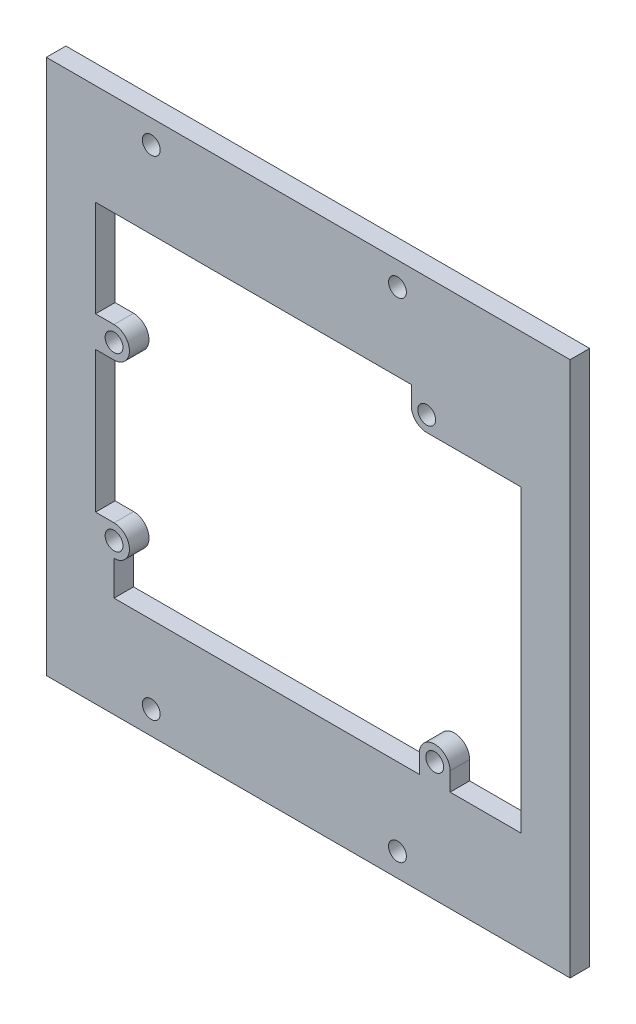
SolidWorks part; units mm, degrees
material "6061-T6 (SS)"
ref_plane "Front Plane" through (0, 0, 0) normal (0, 0, 1) x (1, 0, 0)
ref_plane "Top Plane" through (0, 0, 0) normal (0, 1, 0) x (1, 0, 0)
ref_plane "Right Plane" through (0, 0, 0) normal (1, 0, 0) x (0, 0, -1)
sketch "Sketch1" plane through (0, 0, 0) normal (0, 0, 1) x (1, 0, 0)
  line L0 (24.75, 24.1) -> (26.05, 24.1) construction
  line L1 (-38.75, -43.5) -> (38.75, -43.5) construction
  line L2 (26.05, 24.1) -> (26.05, -24.1) construction
  line L3 (26.05, 0) -> (0, 0) construction
  line L4 (-26.05, -19) -> (26.05, -19) construction
  line L5 (0, 0) -> (0, -19) construction
  line L6 (38.75, -43.5) -> (38.75, 43.5) construction
  line L7 (38.75, 43.5) -> (-38.75, 43.5) construction
  line L8 (-38.75, 43.5) -> (-38.75, 0) construction
  line L9 (-26.05, 6.4) -> (-29.05, 6.4)
  line L10 (-29.05, 6.4) -> (-29.05, -16.5)
  line L11 (-29.05, -16.5) -> (-26.05, -16.5)
  line L12 (-38.75, 0) -> (-38.75, -43.5)
  line L13 (0, 0) -> (-38.75, 0) construction
  line L14 (0, 0) -> (0, -43.5) construction
  line L15 (-26.05, -21.5) -> (-26.05, -27.1)
  line L16 (22.25, 27.1) -> (22.25, 24.1)
  line L17 (-37.05, 43.5) -> (-37.05, -43.5)
  line L18 (-26.05, -27.1) -> (23.55, -27.1)
  line L19 (23.55, -27.1) -> (23.55, -24.1)
  line L20 (28.55, -24.1) -> (28.55, -27.1)
  line L21 (40.05, -27.1) -> (40.05, 21.6)
  line L22 (28.55, -27.1) -> (40.05, -27.1)
  line L23 (-37.05, 43.5) -> (48.05, 43.5)
  line L24 (-37.05, -43.5) -> (48.05, -43.5)
  line L25 (22.25, 27.1) -> (-29.05, 27.1)
  line L26 (-29.05, 27.1) -> (-29.05, 11.4)
  line L27 (-29.05, 11.4) -> (-26.05, 11.4)
  line L29 (48.05, -43.5) -> (48.05, 43.5)
  line L33 (0, 0) -> (0, 43.5) construction
  line L34 (24.75, 21.6) -> (40.05, 21.6)
  circle A0 centre (-20, 39.6925) radius 1.45
  circle A1 centre (-20, -39.6925) radius 1.45
  circle A2 centre (20, -39.6925) radius 1.45
  circle A3 centre (20, 39.6925) radius 1.45
  circle A4 centre (-26.05, 8.9) radius 1.45
  circle A5 centre (-26.05, -19) radius 1.45
  circle A6 centre (24.75, 24.1) radius 1.45
  circle A7 centre (26.05, -24.1) radius 1.45
  arc A8 (-26.05, -16.5) -> (-26.05, -21.5) centre (-26.05, -19) cw
  arc A9 (-26.05, 11.4) -> (-26.05, 6.4) centre (-26.05, 8.9) cw
  arc A10 (28.55, -24.1) -> (23.55, -24.1) centre (26.05, -24.1) ccw
  arc A11 (22.25, 24.1) -> (24.75, 21.6) centre (24.75, 24.1) ccw
  dimension "D2" = 2.9
  dimension "D5" = 27.9
  dimension "D6" = 50.8
  dimension "D7" = 1.3
  dimension "D11" = 2.5
  dimension "D1" = 87
  dimension "D3" = 20
  dimension "D4" = 39.6925
  dimension "D8" = 5.1
  dimension "D9" = 15.2
  dimension "D10" = 14
  dimension "D12" = 14
  dimension "D13" = 3
  dimension "D14" = 3
  dimension "D15" = 3
  dimension "D18" = 8
  dimension "D19" = 8
extrude "Boss-Extrude1" add sketch "Sketch1" along normal blind 3.175
